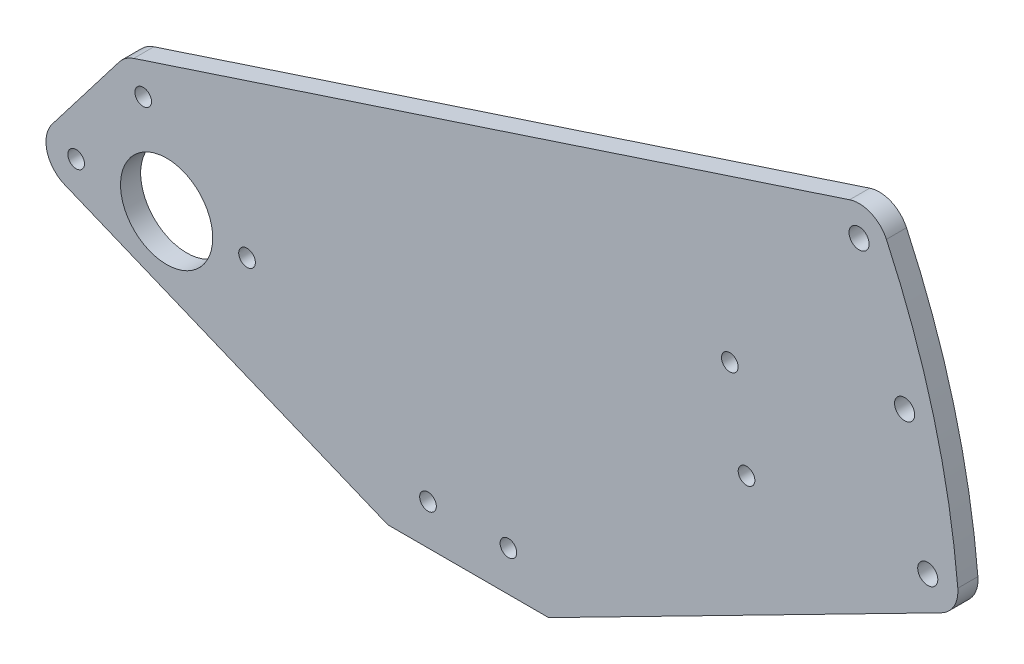
SolidWorks part; units mm, degrees
material "6061-T6 (SS)"
ref_plane "Front Plane" through (0, 0, 0) normal (0, 0, 1) x (1, 0, 0)
ref_plane "Top Plane" through (0, 0, 0) normal (0, 1, 0) x (1, 0, 0)
ref_plane "Right Plane" through (0, 0, 0) normal (1, 0, 0) x (0, 0, -1)
sketch "Sketch1" plane through (0, 0, 0) normal (0, 0, 1) x (1, 0, 0)
  line L0 (0, 0) -> (-28.575, 0) construction
  line L1 (0, 0) -> (-7.3958, 27.6013) construction
  line L2 (0, 0) -> (240.3818, 21.0307) construction
  line L3 (0, 0) -> (25.4, 0) construction
  line L4 (0, 0) -> (240.3818, 21.0307) construction
  line L5 (0, 0) -> (233.0779, 62.453) construction
  line L6 (-36.1317, 5.7985) -> (-14.9524, 33.3998)
  line L7 (-32.1995, -8.8084) -> (69.85, -50.8)
  line L8 (-10.3723, 36.6493) -> (215.7155, 111.0258)
  line L10 (0, 0) -> (0, -38.1) construction
  line L11 (0, -38.1) -> (233.0779, -38.1) construction
  line L12 (82.55, -38.1) -> (107.95, -38.1) construction
  line L13 (69.85, -50.8) -> (120.65, -50.8)
  line L14 (120.65, -50.8) -> (244.7133, 12.5476)
  line L15 (0, 0) -> (177.8752, 47.6615) construction
  line L16 (0, 0) -> (183.1412, 19.2489) construction
  line L17 (0, 0) -> (64.7315, 0) construction
  circle A0 centre (0, 0) radius 14.5542
  circle A1 centre (-28.575, 0) radius 2.6289
  circle A2 centre (-7.3958, 27.6013) radius 2.6289
  circle A3 centre (240.3818, 21.0307) radius 3.175
  circle A4 centre (233.0779, 62.453) radius 3.175
  circle A5 centre (218.6921, 101.9778) radius 3.175
  arc A7 (-32.1995, -8.8084) -> (-36.1317, 5.7985) centre (-28.575, 0) cw
  arc A8 (-10.3723, 36.6493) -> (-14.9524, 33.3998) centre (-7.3958, 27.6013) ccw
  arc A9 (227.3247, 106.0032) -> (215.7155, 111.0258) centre (218.6921, 101.9778) ccw
  arc A10 (227.3247, 106.0032) -> (249.8705, 21.8608) centre (0, 0) cw
  arc A11 (249.8705, 21.8608) -> (244.7133, 12.5476) centre (240.3818, 21.0307) cw
  circle A12 centre (82.55, -38.1) radius 2.6289
  circle A13 centre (107.95, -38.1) radius 2.6289
  circle A14 centre (25.4, 0) radius 2.6289
  circle A15 centre (177.8752, 47.6615) radius 2.6289
  circle A16 centre (183.1412, 19.2489) radius 2.6289
  dimension "D1" = 29.1084
  dimension "D3" = 5.2578
  dimension "D6" = 5.2578
  dimension "D9" = 6.35
  dimension "D12" = 9.525
  dimension "D13" = 9.525
  dimension "D14" = 12.7
  dimension "D15" = 9.525
  dimension "D17" = 5.2578
  dimension "D18" = 5.2578
  dimension "D19" = 82.55
  dimension "D20" = 25.4
  dimension "D22" = 12.7
  dimension "D24" = 5.2578
  dimension "D27" = 5.2578
  dimension "D29" = 5.2578
  dimension "D2" = 28.575
  dimension "D4" = 75
  dimension "D5" = 28.575
  dimension "D7" = 5
  dimension "D8" = 241.3
  dimension "D11" = 10
  dimension "D16" = 38.1
  dimension "D21" = 12.7
  dimension "D23" = 25.4
  dimension "D25" = 15
  dimension "D26" = 184.15
  dimension "D28" = 6
  dimension "D30" = 184.15
  dimension "D10" = 3
extrude "Boss-Extrude1" add sketch "Sketch1" along normal blind 6.35
